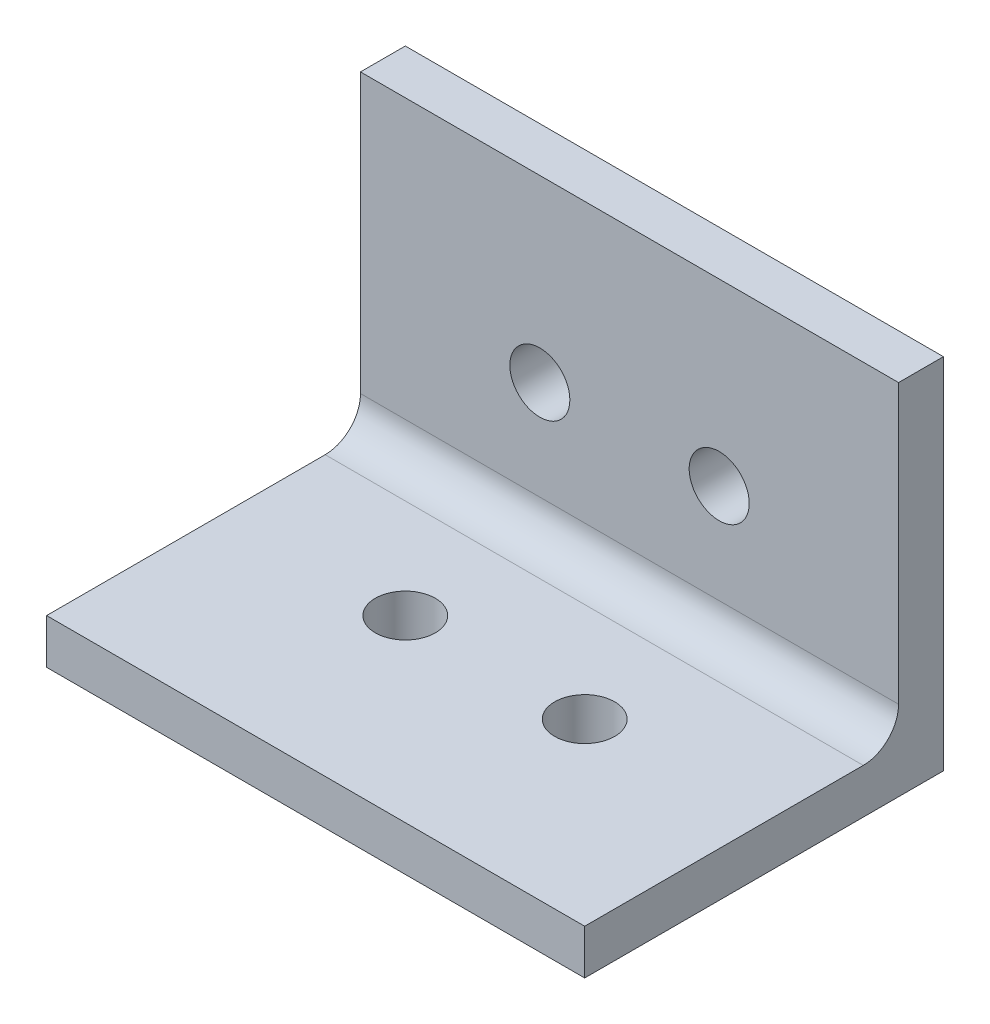
SolidWorks part; units mm, degrees
ref_plane "Front Plane" through (0, 0, 0) normal (0, 0, 1) x (1, 0, 0)
ref_plane "Top Plane" through (0, 0, 0) normal (0, 1, 0) x (1, 0, 0)
ref_plane "Right Plane" through (0, 0, 0) normal (1, 0, 0) x (0, 0, -1)
sketch "Sketch1" plane through (0, 0, 0) normal (1, 0, 0) x (0, 0, -1)
  line L0 (0, 0) -> (0, 50.8)
  line L1 (0, 50.8) -> (-6.35, 50.8)
  line L2 (-6.35, 50.8) -> (-6.35, 6.35)
  line L3 (-6.35, 6.35) -> (-50.8, 6.35)
  line L4 (-50.8, 6.35) -> (-50.8, 0)
  line L5 (-50.8, 0) -> (0, 0)
  dimension "D1" = 50.8
  dimension "D2" = 50.8
  dimension "D3" = 6.35
  dimension "D4" = 6.35
extrude "Boss-Extrude1" add sketch "Sketch1" along normal blind 76.2
sketch "Sketch2" plane through (0, 6.35, 0) normal (0, 1, 0) x (1, 0, 0)
  line L0 (76.2, -50.8) -> (0, -50.8) construction
  point P0 (25.4, -25.4)
  dimension "D1" = 25.4
sketch "Sketch4" plane through (0, 0, 6.35) normal (0, 0, 1) x (1, 0, 0)
  line L0 (25.4, 50.8) -> (25.4, 6.2679) construction
  line L1 (76.2, 50.8) -> (0, 50.8) construction
  line L4 (76.2, 6.35) -> (0, 6.35) construction
  line L5 (0, 50.8) -> (0, 6.35) construction
  line L6 (50.8, 50.8) -> (50.8, 6.35) construction
  line L7 (76.2, 50.8) -> (76.2, 6.35) construction
  point P6 (25.4, 25.4)
  point P13 (50.8, 6.35)
  point P14 (50.8, 6.35)
  point P15 (50.8, 25.4)
  dimension "D1" = 25.4
  dimension "D2" = 25.4
  dimension "D3" = 25.4
  dimension "D4" = 25.4
hole_wizard "Tap Drill for M10x1.5 Tap1" positions "Sketch6" profile "Sketch7" hole size "M10x1.5" standard "ANSI Metric" end condition through all
sketch "Sketch6" plane through (0, 6.35, 0) normal (0, 1, 0) x (1, 0, 0)
  line L1 (76.2, -6.35) -> (76.2, -50.8) construction
  point P0 (25.4, -25.4)
  point P9 (50.8, -25.4)
  dimension "D1" = 25.4
sketch "Sketch7" plane through (25.4, 6.35, 25.4) normal (1, 0, 0) x (0, 0, 1)
  line L0 (0, 0) -> (0, 6.35)
  line L1 (0, 6.35) -> (4.25, 6.35)
  line L2 (4.25, 6.35) -> (4.25, 0)
  line L5 (4.25, 0) -> (0, 0)
  line L11 (0, -6.35) -> (0, 107.95) construction
  dimension "Thru Hole Dia." = 8.5
  dimension "Thru Hole Depth" = 6.35
hole_wizard "Tap Drill for M10x1.5 Tap2" positions "Sketch9" profile "Sketch8" hole size "M10x1.5" standard "ANSI Metric"
sketch "Sketch9" plane through (0, 0, 6.35) normal (0, 0, 1) x (1, 0, 0)
  point P0 (25.4, 25.4)
  point P4 (50.8, 25.4)
sketch "Sketch8" plane through (25.4, 25.4, 6.35) normal (1, 0, 0) x (0, -1, 0)
  line L0 (0, 0) -> (0, 22.5537)
  line L1 (0, 22.5537) -> (4.25, 20)
  line L2 (4.25, 20) -> (4.25, 0)
  line L5 (4.25, 0) -> (0, 0)
  line L10 (0, 22.5537) -> (-4.25, 20) construction
  line L11 (0, -6.35) -> (0, 107.95) construction
  dimension "Hole Dia." = 8.5
  dimension "Hole Depth" = 20
  dimension "Drill Angle" = 118
fillet "Fillet1" radius 5 1 edges at (38.1, 6.35, 6.35)
